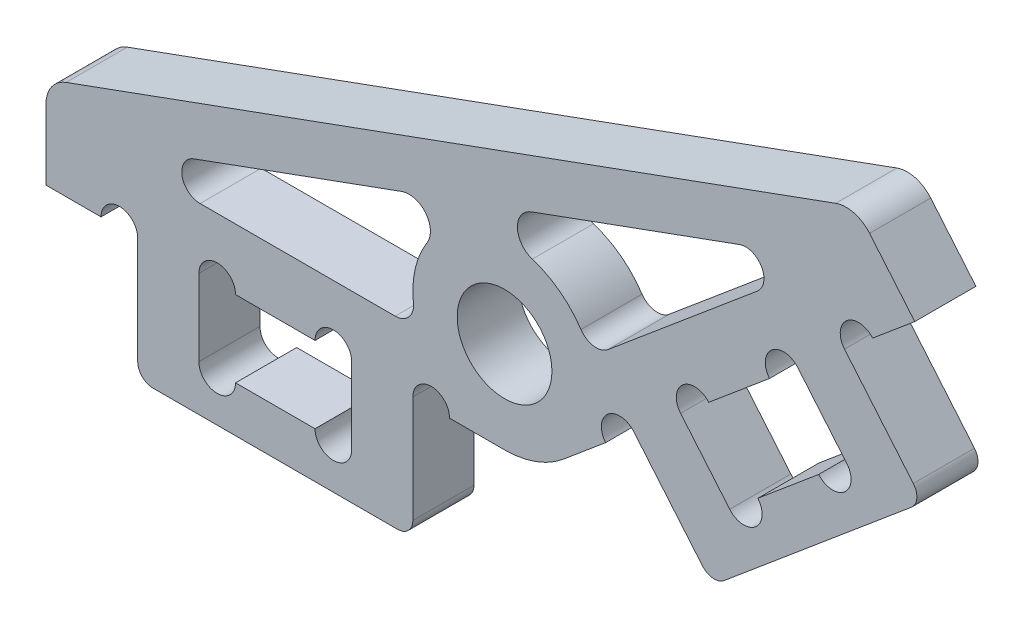
SolidWorks part; units mm, degrees
ref_plane "前视基准面" through (0, 0, 0) normal (0, 0, 1) x (1, 0, 0)
ref_plane "上视基准面" through (0, 0, 0) normal (0, 1, 0) x (1, 0, 0)
ref_plane "右视基准面" through (0, 0, 0) normal (1, 0, 0) x (0, 0, -1)
sketch "草图1" plane through (0, 0, 0) normal (0, 0, 1) x (1, 0, 0)
  line L0 (0, -3) -> (-15, -3)
  line L1 (1.9284, -2.2981) -> (13.419, 7.3437)
  line L2 (-15, -3) -> (-15, 0)
  line L3 (-15, 0) -> (11.4907, 9.6418)
  line L4 (11.4907, 9.6418) -> (13.419, 7.3437)
  line L5 (-13.3618, -1) -> (-3.3645, 2.6387)
  line L6 (-13.3618, -1) -> (-2.8284, -1)
  line L7 (-1.7547, 4.8209) -> (0, 0) construction
  line L10 (10.8785, 7.8227) -> (2.8095, 1.052)
  line L11 (10.8785, 7.8227) -> (0.8812, 4.184)
  arc A0 (0, -3) -> (1.9284, -2.2981) centre (0, 0) ccw
  circle A1 centre (0, 0) radius 1.55
  arc A2 (-2.5338, 1.6062) -> (-2.8284, -1) centre (0, 0) ccw
  arc A4 (-2.5338, 1.6062) -> (-3.3645, 2.6387) centre (-3.125, 1.9809) ccw
  arc A5 (0.9086, 2.8591) -> (2.8095, 1.052) centre (0, 0) cw
  arc A6 (0.9086, 2.8591) -> (0.8812, 4.184) centre (1.1206, 3.5262) cw
  point P20 (12.1642, 9.2753)
  dimension "D1" = 0.7
  dimension "D2" = 3.1
  dimension "D3" = 6
  dimension "D7" = 2
  dimension "D9" = 140
  dimension "D4" = 15
  dimension "D5" = 15
  dimension "D6" = 3
  dimension "D8" = 1.5
extrude "凸台-拉伸1" add sketch "草图1" along normal mid plane 2
fillet "圆角1" radius 0.6 4 edges at (-13.3618, -1, 0) (-2.8284, -1, 0) (2.8095, 1.052, 0) (10.8785, 7.8227, 0)
sketch "草图2" plane through (0, 0, 1) normal (0, 0, 1) x (1, 0, 0)
  line L0 (-15, -3) -> (0, -3) construction
  line L1 (-12, -3) -> (-10, -3)
  line L2 (-12, -3) -> (-12, -7)
  line L3 (-12, -7) -> (-3, -7)
  line L4 (-3, -3) -> (-3, -7)
  line L5 (-10, -3) -> (-10, -5.5)
  line L6 (-10, -5.5) -> (-5, -5.5)
  line L7 (-5, -5.5) -> (-5, -3)
  line L8 (-5, -3) -> (-3, -3)
  line L9 (-7.5, -7) -> (-7.5, -3) construction
  line L10 (0, 0) -> (-1.7547, 4.8209) construction
  line L11 (11.4907, 9.6418) -> (-15, 0) construction
  line L12 (11.1209, 5.4153) -> (13.692, 2.3511)
  line L13 (13.692, 2.3511) -> (6.7976, -3.4339)
  line L14 (4.2265, -0.3698) -> (6.7976, -3.4339)
  line L15 (5.7586, 0.9158) -> (4.2265, -0.3698)
  line L16 (7.3656, -0.9993) -> (5.7586, 0.9158)
  line L17 (11.1958, 2.2146) -> (7.3656, -0.9993)
  line L18 (9.5888, 4.1297) -> (11.1958, 2.2146)
  line L19 (11.1209, 5.4153) -> (9.5888, 4.1297)
  dimension "D1" = 9
  dimension "D2" = 5
  dimension "D3" = 2.5
  dimension "D4" = 4
extrude "凸台-拉伸2" add sketch "草图2" against normal blind 2
sketch "草图3" plane through (0, 0, 1) normal (0, 0, 1) x (1, 0, 0)
  line L0 (-10, -3) -> (-5, -3) construction
  line L1 (-5, -5.5) -> (-10, -5.5) construction
  line L2 (5.7586, 0.9158) -> (9.5888, 4.1297) construction
  line L3 (11.1958, 2.2146) -> (7.3656, -0.9993) construction
  line L4 (-15, -3) -> (-12, -3) construction
  line L5 (-3, -3) -> (0, -3) construction
  line L6 (1.9284, -2.2981) -> (4.2265, -0.3698) construction
  line L7 (11.1209, 5.4153) -> (13.419, 7.3437) construction
  circle A0 centre (-5.6, -3) radius 0.6
  circle A1 centre (-5.6, -5.5) radius 0.6
  circle A2 centre (-9.4, -3) radius 0.6
  circle A3 centre (-9.4, -5.5) radius 0.6
  circle A4 centre (6.2182, 1.3015) radius 0.6
  circle A5 centre (7.8252, -0.6136) radius 0.6
  circle A6 centre (9.1292, 3.7441) radius 0.6
  circle A7 centre (10.7361, 1.829) radius 0.6
  circle A8 centre (-12.6, -3) radius 0.6
  circle A9 centre (-2.4, -3) radius 0.6
  circle A10 centre (3.7669, -0.7554) radius 0.6
  circle A11 centre (11.5805, 5.801) radius 0.6
  dimension "D1" = 1.2
extrude "切除-拉伸1" cut sketch "草图3" against normal through all
fillet "圆角2" radius 0.5 4 edges at (13.692, 2.3511, 0) (6.7976, -3.4339, 0) (-3, -7, 0) (-12, -7, 0)
fillet "圆角3" radius 1 2 edges at (11.4907, 9.6418, 0) (-15, 0, 0)
